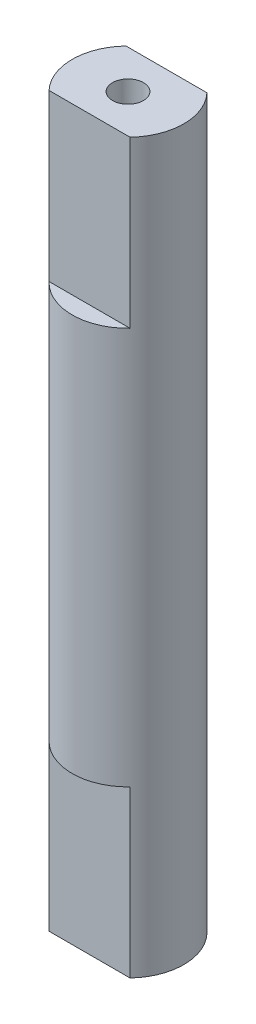
SolidWorks part; units mm, degrees
material "Nylon 101"
ref_plane "Plan de face" through (0, 0, 0) normal (0, 0, 1) x (1, 0, 0)
ref_plane "Plan de dessus" through (0, 0, 0) normal (0, 1, 0) x (1, 0, 0)
ref_plane "Plan de droite" through (0, 0, 0) normal (1, 0, 0) x (0, 0, -1)
sketch "Esquisse1" plane through (0, 0, 0) normal (0, 0, 1) x (1, 0, 0)
  line L0 (0, 24.6045) -> (0, -23.1859) construction
  line L1 (-18.0959, 0) -> (15.5968, 0) construction
  line L2 (-2.7, 17.6) -> (-2.7, -17.6)
  line L3 (-2.7, -17.6) -> (-0.75, -17.6)
  line L4 (-0.75, -17.6) -> (-0.75, -9.6)
  line L5 (-0.75, -9.6) -> (0, -9.167)
  line L6 (0, -9.167) -> (0, 9.167)
  line L7 (0, 9.167) -> (-0.75, 9.6)
  line L8 (-0.75, 9.6) -> (-0.75, 17.6)
  line L9 (-0.75, 17.6) -> (-2.7, 17.6)
  dimension "D1" = 35.2
  dimension "D2" = 2.7
  dimension "D3" = 0.75
  dimension "D4" = 8
  dimension "D5" = 60
  dimension "D6" = 8
revolve "Révolution1" add sketch "Esquisse1" angle 360 about L0
sketch "Esquisse2" plane through (0, 17.6, 0) normal (0, 1, 0) x (1, 0, 0)
  line L0 (-3.639, 0) -> (3.4285, 0) construction
  line L1 (0, -3.4494) -> (0, 4.5798) construction
  line L2 (-2, 1.86) -> (2, 1.86)
  line L3 (-2, 1.86) -> (-2, 2.86)
  line L4 (-2, 2.86) -> (2, 2.86)
  line L5 (2, 1.86) -> (2, 2.86)
  line L6 (2, -1.86) -> (2, -2.86)
  line L7 (-2, -2.86) -> (2, -2.86)
  line L8 (-2, -1.86) -> (-2, -2.86)
  line L9 (-2, -1.86) -> (2, -1.86)
  dimension "D1" = 1.86
  dimension "D2" = 1
  dimension "D3" = 4
extrude "Enlèv. mat.-Extru.1" cut sketch "Esquisse2" against normal blind 8
mirror "Symétrie1" about plane through (0, 0, 0) normal (0, 1, 0) of "Enlèv. mat.-Extru.1"
